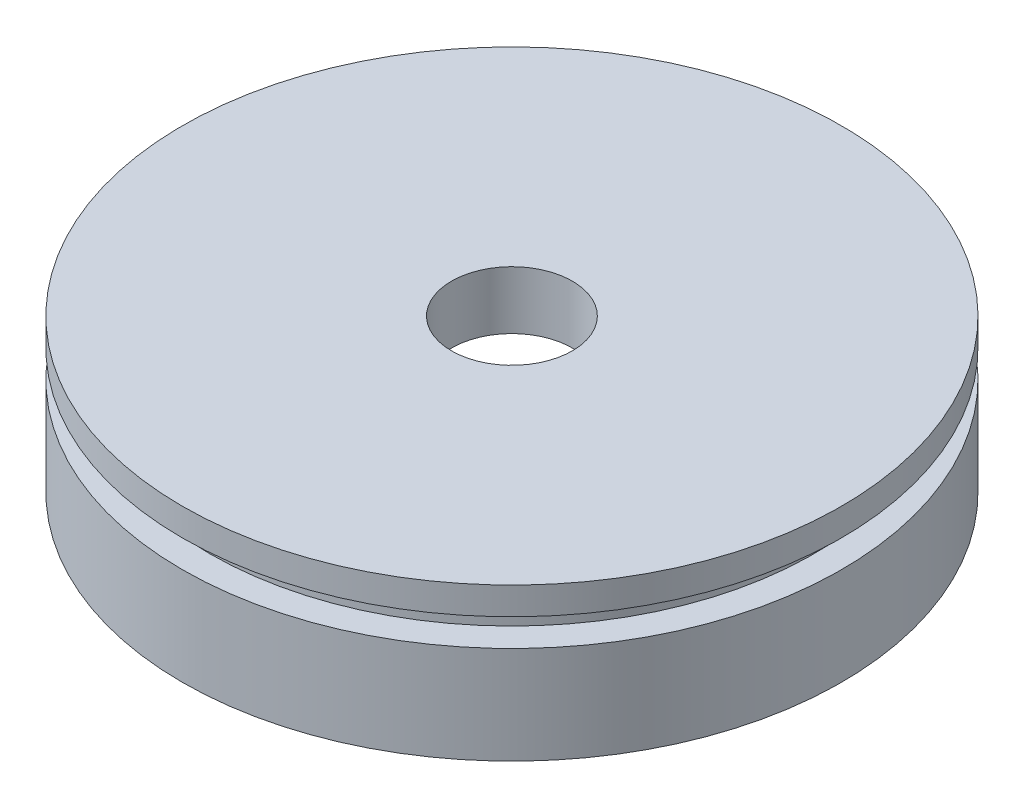
SolidWorks part; units mm, degrees
material "Silicon Rubber"
ref_plane "Front Plane" through (0, 0, 0) normal (0, 0, 1) x (1, 0, 0)
ref_plane "Top Plane" through (0, 0, 0) normal (0, 1, 0) x (1, 0, 0)
ref_plane "Right Plane" through (0, 0, 0) normal (1, 0, 0) x (0, 0, -1)
sketch "Sketch1" plane through (0, 0, 0) normal (0, 0, 1) x (1, 0, 0)
  line L3 (0, 50.358) -> (0, -222.3667) construction
  line L16 (-69.85, 1876.044) -> (-69.85, 1869.694)
  line L17 (-69.85, 1876.044) -> (-76.2, 1876.044)
  line L18 (-76.2, 1876.044) -> (-76.2, 1882.394)
  line L19 (-76.2, 1882.394) -> (-13.97, 1882.394)
  line L20 (-69.85, 1869.694) -> (-76.2, 1869.694)
  line L24 (0, 1882.394) -> (0, 1869.694) construction
  line L25 (-76.2, 1847.1312) -> (-76.2, 1869.694)
  line L26 (-13.97, 1882.394) -> (-13.97, 1868.995)
  arc A2 (-76.2, 1847.1312) -> (-13.97, 1868.995) centre (0, 1729.74) cw
  point P5 (0, 0)
  point P15 (0, 0)
  point P16 (0, 0)
  dimension "D5" = 13.97
  dimension "D6" = 6.35
  dimension "D1" = 139.954
  dimension "D2" = 76.2
  dimension "D3" = 12.7
  dimension "D4" = 6.35
  dimension "D7" = 62.23
  dimension "D8" = 6.35
  dimension "D9" = 139.954
  dimension "D10" = 6.35
revolve "Revolve1" add sketch "Sketch1" angle 360 about L3
equation "\"OD\"=5.25"
equation "\"t_wrap\"=0.131"
equation "\"t_wall\"=0.511"
